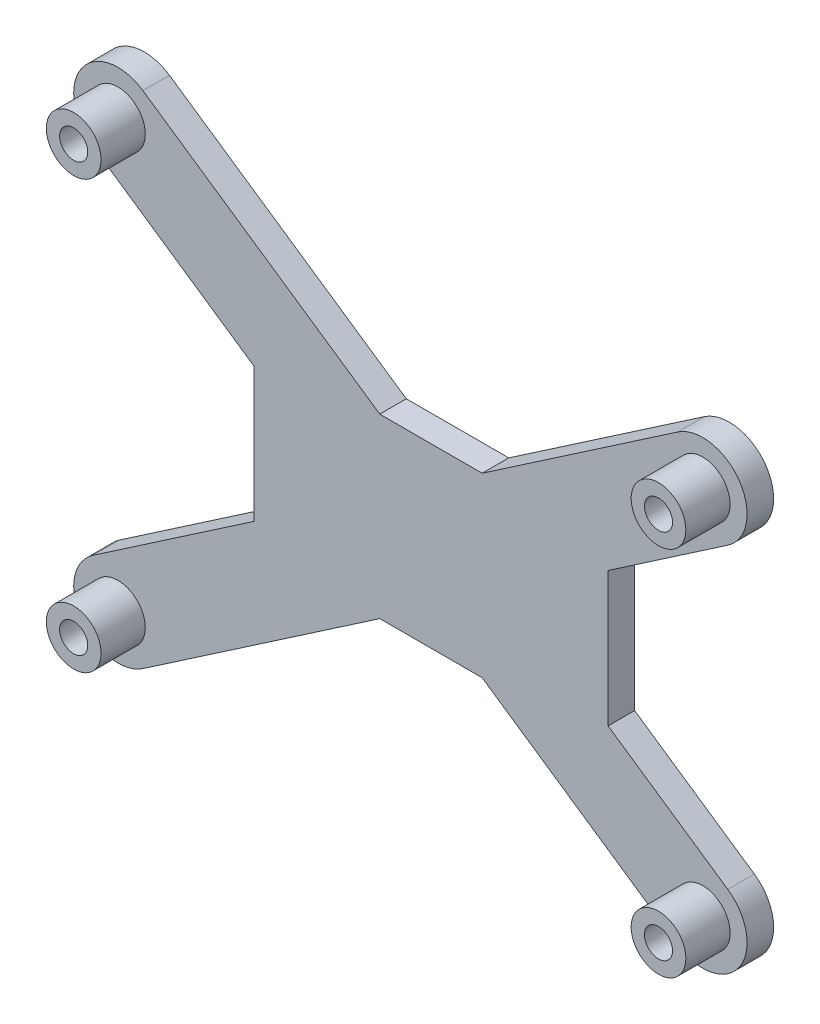
SolidWorks part; units mm, degrees
ref_plane "Front Plane" through (0, 0, 0) normal (0, 0, 1) x (1, 0, 0)
ref_plane "Top Plane" through (0, 0, 0) normal (0, 1, 0) x (1, 0, 0)
ref_plane "Right Plane" through (0, 0, 0) normal (1, 0, 0) x (0, 0, -1)
sketch "Sketch3" plane through (0, 0, 0) normal (0, 0, 1) x (1, 0, 0)
  line L154 (-0.0227, 48.26) -> (-0.0227, 37.973)
  line L155 (-0.0227, 37.973) -> (10.5443, 37.973)
  line L156 (12.0617, 37.973) -> (19.0628, 37.973)
  line L157 (19.0628, 37.973) -> (19.0628, 21.717)
  line L158 (19.0628, 21.717) -> (12.0617, 21.717)
  line L159 (10.5443, 21.717) -> (-0.0227, 21.717)
  line L160 (-0.0227, 21.717) -> (-0.0227, 6.35)
  line L161 (-0.0227, 6.35) -> (0.0173, 5.6365)
  line L162 (0.0173, 5.6365) -> (0.1371, 4.9319)
  line L163 (0.1371, 4.9319) -> (0.3349, 4.2452)
  line L164 (0.3349, 4.2452) -> (0.6084, 3.585)
  line L165 (0.6084, 3.585) -> (0.9541, 2.9595)
  line L166 (0.9541, 2.9595) -> (1.3676, 2.3767)
  line L167 (1.3676, 2.3767) -> (1.8438, 1.8438)
  line L168 (1.8438, 1.8438) -> (2.3767, 1.3676)
  line L169 (2.3767, 1.3676) -> (2.9595, 0.9541)
  line L170 (2.9595, 0.9541) -> (3.585, 0.6084)
  line L171 (3.585, 0.6084) -> (4.2452, 0.3349)
  line L172 (4.2452, 0.3349) -> (4.9319, 0.1371)
  line L173 (4.9319, 0.1371) -> (5.6365, 0.0173)
  line L174 (5.6365, 0.0173) -> (6.35, -0.0227)
  line L175 (6.35, -0.0227) -> (6.35, -0.0127)
  line L176 (6.35, -0.0127) -> (73.66, -0.0248)
  line L177 (73.66, -0.0248) -> (74.769, 0.0236)
  line L178 (74.769, 0.0236) -> (75.8696, 0.1685)
  line L179 (75.8696, 0.1685) -> (76.9534, 0.4088)
  line L180 (76.9534, 0.4088) -> (78.0121, 0.7426)
  line L181 (78.0121, 0.7426) -> (79.0377, 1.1674)
  line L182 (79.0377, 1.1674) -> (80.0224, 1.68)
  line L183 (80.0224, 1.68) -> (80.9587, 2.2764)
  line L184 (80.9587, 2.2764) -> (81.8394, 2.9522)
  line L185 (81.8394, 2.9522) -> (82.6578, 3.7022)
  line L186 (82.6578, 3.7022) -> (83.4078, 4.5206)
  line L187 (83.4078, 4.5206) -> (84.0836, 5.4013)
  line L188 (84.0836, 5.4013) -> (84.68, 6.3376)
  line L189 (84.68, 6.3376) -> (85.1926, 7.3223)
  line L190 (85.1926, 7.3223) -> (85.6174, 8.3479)
  line L191 (85.6174, 8.3479) -> (85.9512, 9.4066)
  line L192 (85.9512, 9.4066) -> (86.1915, 10.4904)
  line L193 (86.1915, 10.4904) -> (86.3364, 11.591)
  line L194 (86.3364, 11.591) -> (86.3848, 12.7)
  line L195 (86.3848, 12.7) -> (86.3727, 12.7)
  line L196 (86.3727, 12.7) -> (86.3848, 41.91)
  line L197 (86.3848, 41.91) -> (86.3364, 43.019)
  line L198 (86.3364, 43.019) -> (86.1915, 44.1196)
  line L199 (86.1915, 44.1196) -> (85.9512, 45.2034)
  line L200 (85.9512, 45.2034) -> (85.6174, 46.2621)
  line L201 (85.6174, 46.2621) -> (85.1926, 47.2877)
  line L202 (85.1926, 47.2877) -> (84.68, 48.2724)
  line L203 (84.68, 48.2724) -> (84.0836, 49.2087)
  line L204 (84.0836, 49.2087) -> (83.4078, 50.0894)
  line L205 (83.4078, 50.0894) -> (82.6578, 50.9078)
  line L206 (82.6578, 50.9078) -> (81.8394, 51.6578)
  line L207 (81.8394, 51.6578) -> (80.9587, 52.3336)
  line L208 (80.9587, 52.3336) -> (80.0224, 52.93)
  line L209 (80.0224, 52.93) -> (79.0377, 53.4426)
  line L210 (79.0377, 53.4426) -> (78.0121, 53.8674)
  line L211 (78.0121, 53.8674) -> (76.9534, 54.2012)
  line L212 (76.9534, 54.2012) -> (75.8696, 54.4415)
  line L213 (75.8696, 54.4415) -> (74.769, 54.5864)
  line L214 (74.769, 54.5864) -> (73.66, 54.6348)
  line L215 (73.66, 54.6348) -> (73.66, 54.6227)
  line L216 (73.66, 54.6227) -> (6.35, 54.6327)
  line L217 (6.35, 54.6327) -> (5.6365, 54.5927)
  line L218 (5.6365, 54.5927) -> (4.9319, 54.4729)
  line L219 (4.9319, 54.4729) -> (4.2452, 54.2751)
  line L220 (4.2452, 54.2751) -> (3.585, 54.0016)
  line L221 (3.585, 54.0016) -> (2.9595, 53.6559)
  line L222 (2.9595, 53.6559) -> (2.3767, 53.2424)
  line L223 (2.3767, 53.2424) -> (1.8438, 52.7662)
  line L224 (1.8438, 52.7662) -> (1.3676, 52.2333)
  line L225 (1.3676, 52.2333) -> (0.9541, 51.6505)
  line L226 (0.9541, 51.6505) -> (0.6084, 51.025)
  line L227 (0.6084, 51.025) -> (0.3349, 50.3648)
  line L228 (0.3349, 50.3648) -> (0.1371, 49.6781)
  line L229 (0.1371, 49.6781) -> (0.0173, 48.9735)
  line L230 (0.0173, 48.9735) -> (-0.0227, 48.26)
  arc A6 (11.5782, 38.4703) -> (10.5443, 37.973) centre (11.303, 37.719) ccw
  arc A7 (12.0617, 37.973) -> (11.6982, 38.4147) centre (11.303, 37.719) ccw
  arc A8 (10.5443, 21.717) -> (12.0617, 21.717) centre (11.303, 21.971) ccw
  circle A10 centre (14.605, 3.175) radius 1.5875
  circle A11 centre (14.605, 51.435) radius 1.5875
  circle A12 centre (80.645, 48.26) radius 1.5875
  circle A13 centre (80.645, 6.35) radius 1.5875
  spline S14 degree 3 poles (11.5782, 38.4703) (11.5632, 38.4791) (11.5278, 38.502) (11.4744, 38.5437) (11.4201, 38.5963) (11.371, 38.6535) (11.3276, 38.7136) (11.2911, 38.7761) (11.2612, 38.8412) (11.2378, 38.9085) (11.2215, 38.9783) (11.2111, 39.0503) (11.2099, 39.0992) (11.2094, 39.124) knots 0.340647 0.340647 0.340647 0.340647 0.384555 0.446913 0.510958 0.574931 0.636685 0.697483 0.757134 0.816966 0.876818 0.937663 1 1 1 1
  spline S15 degree 3 poles (11.2094, 39.124) (11.21, 39.1484) (11.2113, 39.1969) (11.2206, 39.2683) (11.2363, 39.3372) (11.2584, 39.4035) (11.2867, 39.4673) (11.3212, 39.5287) (11.3622, 39.5876) (11.3937, 39.624) (11.4097, 39.6424) knots 0 0 0 0 0.128919 0.255238 0.378679 0.501088 0.622714 0.746241 0.871589 1 1 1 1
  spline S16 degree 3 poles (11.4097, 39.6424) (11.4282, 39.6618) (11.4647, 39.7) (11.5261, 39.7489) (11.5903, 39.7911) (11.6588, 39.8251) (11.7306, 39.8519) (11.8061, 39.8705) (11.8851, 39.8826) (11.9392, 39.8838) (11.9666, 39.8844) knots 0 0 0 0 0.128498 0.252713 0.374819 0.496436 0.617911 0.741288 0.8687 1 1 1 1
  spline S17 degree 3 poles (11.9666, 39.8844) (11.994, 39.8838) (12.0478, 39.8827) (12.1265, 39.8704) (12.2017, 39.8517) (12.2736, 39.8259) (12.3413, 39.7912) (12.4057, 39.7498) (12.4667, 39.7008) (12.5033, 39.6629) (12.5219, 39.6436) knots 0 0 0 0 0.131751 0.258332 0.382134 0.503804 0.624693 0.746871 0.871514 1 1 1 1
  spline S18 degree 3 poles (12.5219, 39.6436) (12.5379, 39.6252) (12.5695, 39.5887) (12.6102, 39.5296) (12.6451, 39.4684) (12.6732, 39.4043) (12.6953, 39.3378) (12.711, 39.2687) (12.7203, 39.1972) (12.7216, 39.1486) (12.7222, 39.124) knots 0 0 0 0 0.128157 0.253834 0.376506 0.498534 0.621368 0.744565 0.870634 1 1 1 1
  spline S19 degree 3 poles (12.7222, 39.124) (12.7216, 39.0992) (12.7205, 39.0503) (12.7101, 38.9783) (12.6938, 38.9085) (12.6704, 38.8412) (12.6405, 38.7761) (12.604, 38.7136) (12.5606, 38.6535) (12.5115, 38.5963) (12.4572, 38.5437) (12.3983, 38.4978) (12.3359, 38.4584) (12.2692, 38.4268) (12.1989, 38.4018) (12.1248, 38.3842) (12.0469, 38.3736) (11.9937, 38.3723) (11.9666, 38.3716) knots 0 0 0 0 0.062416 0.123337 0.183265 0.243172 0.302898 0.363774 0.425605 0.489659 0.553785 0.616222 0.677854 0.739517 0.802097 0.865866 0.931508 1 1 1 1
  spline S20 degree 3 poles (11.9666, 38.3716) (11.9393, 38.3723) (11.8859, 38.3736) (11.8078, 38.3842) (11.7456, 38.3989) (11.7098, 38.4106) (11.6982, 38.4147) knots 0 0 0 0 0.068742 0.134635 0.198324 0.229433 0.229433 0.229433 0.229433
sketch "seperate" plane through (0, 0, 0) normal (0, 0, 1) x (1, 0, 0)
  line L0 (14.605, 3.175) -> (80.645, 48.26) construction
  line L1 (11.7859, 7.3045) -> (77.8259, 52.3895)
  line L2 (17.4241, -0.9545) -> (83.4641, 44.1305)
  line L3 (14.605, 51.435) -> (80.645, 6.35) construction
  line L4 (17.4241, 55.5645) -> (83.4641, 10.4795)
  line L5 (11.7859, 47.3055) -> (77.8259, 2.2205)
  line L6 (49.9504, 27.305) -> (49.9504, 37.305) construction
  line L7 (49.9504, 27.305) -> (49.9504, 17.305) construction
  line L8 (49.9504, 37.305) -> (69.9504, 37.305)
  line L9 (49.9504, 37.305) -> (29.9504, 37.305)
  line L10 (49.9504, 17.305) -> (69.9504, 17.305)
  line L11 (49.9504, 17.305) -> (29.9504, 17.305)
  line L12 (69.9504, 37.305) -> (69.9504, 17.305)
  line L13 (29.9504, 37.305) -> (29.9504, 17.305)
  circle A0 centre (14.605, 51.435) radius 1.5875 construction
  circle A1 centre (14.605, 3.175) radius 1.5875 construction
  circle A2 centre (80.645, 6.35) radius 1.5875 construction
  circle A3 centre (80.645, 48.26) radius 1.5875 construction
  circle A4 centre (14.605, 51.435) radius 1.5875
  circle A5 centre (14.605, 3.175) radius 1.5875
  circle A6 centre (80.645, 6.35) radius 1.5875
  circle A7 centre (80.645, 48.26) radius 1.5875
  arc A8 (11.7859, 7.3045) -> (17.4241, -0.9545) centre (14.605, 3.175) ccw
  arc A9 (83.4641, 44.1305) -> (77.8259, 52.3895) centre (80.645, 48.26) ccw
  arc A10 (17.4241, 55.5645) -> (11.7859, 47.3055) centre (14.605, 51.435) ccw
  arc A11 (77.8259, 2.2205) -> (83.4641, 10.4795) centre (80.645, 6.35) ccw
  point P0 (47.625, 25.7175)
  point P1 (80.645, 6.35)
  point P10 (80.645, 48.26)
  point P11 (14.605, 51.435)
  point P12 (14.605, 3.175)
  point P17 (47.625, 28.8925)
  point P26 (49.9504, 27.305)
  point P29 (29.9504, 34.9048)
  point P35 (29.9504, 19.7052)
  point P36 (44.1704, 17.305)
  point P37 (55.7303, 17.305)
  point P38 (69.9504, 19.7052)
  point P39 (69.9504, 34.9048)
  point P40 (55.7303, 37.305)
  point P41 (44.1704, 37.305)
  dimension "D1" = 10
  dimension "D2" = 10
  dimension "D3" = 10
  dimension "D4" = 10
  dimension "D5" = 20
  dimension "D6" = 20
  dimension "D7" = 20
  dimension "D8" = 20
sketch "combination" plane through (0, 0, 0) normal (0, 0, 1) x (1, 0, 0)
  line L0 (17.4241, 55.5645) -> (83.4641, 10.4795) construction
  line L1 (11.7859, 7.3045) -> (77.8259, 52.3895) construction
  line L2 (49.9504, 37.305) -> (69.9504, 37.305) construction
  line L3 (49.9504, 37.305) -> (29.9504, 37.305) construction
  line L4 (29.9504, 37.305) -> (29.9504, 17.305) construction
  line L5 (49.9504, 17.305) -> (29.9504, 17.305) construction
  line L6 (49.9504, 17.305) -> (69.9504, 17.305) construction
  line L7 (69.9504, 37.305) -> (69.9504, 17.305) construction
  line L8 (17.4241, 55.5645) -> (44.1704, 37.305)
  line L9 (11.7859, 7.3045) -> (29.9504, 19.7052)
  line L10 (49.9504, 37.305) -> (55.7303, 37.305)
  line L11 (49.9504, 37.305) -> (44.1704, 37.305)
  line L12 (29.9504, 34.9048) -> (29.9504, 19.7052)
  line L13 (49.9504, 17.305) -> (44.1704, 17.305)
  line L14 (49.9504, 17.305) -> (55.7303, 17.305)
  line L15 (69.9504, 34.9048) -> (69.9504, 19.7052)
  line L16 (17.4241, -0.9545) -> (83.4641, 44.1305) construction
  line L17 (11.7859, 47.3055) -> (77.8259, 2.2205) construction
  line L18 (17.4241, -0.9545) -> (44.1704, 17.305)
  line L19 (11.7859, 47.3055) -> (29.9504, 34.9048)
  line L23 (55.7303, 17.305) -> (77.8259, 2.2205)
  line L24 (69.9504, 19.7052) -> (83.4641, 10.4795)
  line L25 (69.9504, 34.9048) -> (83.4641, 44.1305)
  line L26 (55.7303, 37.305) -> (77.8259, 52.3895)
  circle A0 centre (14.605, 51.435) radius 1.5875 construction
  circle A1 centre (14.605, 3.175) radius 1.5875 construction
  circle A2 centre (80.645, 6.35) radius 1.5875 construction
  circle A3 centre (80.645, 48.26) radius 1.5875 construction
  circle A4 centre (14.605, 51.435) radius 1.5875
  circle A5 centre (14.605, 3.175) radius 1.5875
  circle A6 centre (80.645, 6.35) radius 1.5875
  circle A7 centre (80.645, 48.26) radius 1.5875
  arc A8 (11.7859, 7.3045) -> (17.4241, -0.9545) centre (14.605, 3.175) ccw construction
  arc A9 (11.7859, 7.3045) -> (17.4241, -0.9545) centre (14.605, 3.175) ccw
  arc A10 (77.8259, 2.2205) -> (83.4641, 10.4795) centre (80.645, 6.35) ccw construction
  arc A11 (83.4641, 44.1305) -> (77.8259, 52.3895) centre (80.645, 48.26) ccw construction
  arc A12 (77.8259, 2.2205) -> (83.4641, 10.4795) centre (80.645, 6.35) ccw
  arc A13 (83.4641, 44.1305) -> (77.8259, 52.3895) centre (80.645, 48.26) ccw
  arc A14 (17.4241, 55.5645) -> (11.7859, 47.3055) centre (14.605, 51.435) ccw construction
  arc A15 (17.4241, 55.5645) -> (11.7859, 47.3055) centre (14.605, 51.435) ccw
sketch "Sketch4" plane through (0, 0, 0) normal (0, 0, 1) x (1, 0, 0)
  circle A0 centre (14.605, 3.175) radius 1.5875 construction
  circle A1 centre (14.605, 51.435) radius 1.5875 construction
  circle A2 centre (80.645, 48.26) radius 1.5875 construction
  circle A3 centre (80.645, 6.35) radius 1.5875 construction
  circle A4 centre (14.605, 3.175) radius 1.5875
  circle A5 centre (14.605, 51.435) radius 1.5875
  circle A6 centre (80.645, 48.26) radius 1.5875
  circle A7 centre (80.645, 6.35) radius 1.5875
  circle A8 centre (14.605, 3.175) radius 3.0875
  circle A9 centre (14.605, 51.435) radius 3.0875
  circle A10 centre (80.645, 48.26) radius 3.0875
  circle A11 centre (80.645, 6.35) radius 3.0875
  dimension "D1" = 1.5
extrude "Boss-Extrude1" add sketch "Sketch4" along normal blind 5
extrude "Boss-Extrude2" add sketch "combination" against normal blind 3
